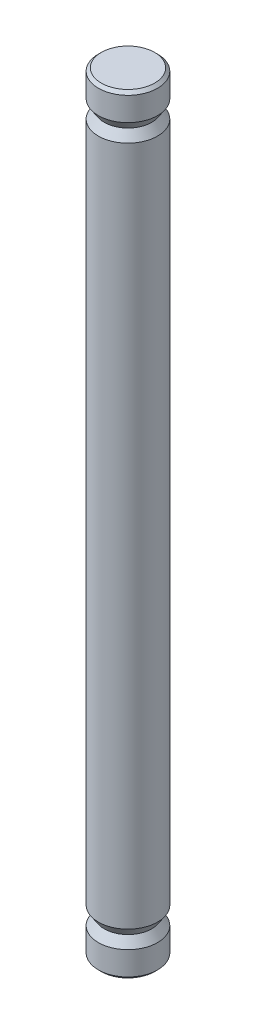
SolidWorks part; units mm, degrees
ref_plane "Plan de face" through (0, 0, 0) normal (0, 0, 1) x (1, 0, 0)
ref_plane "Plan de dessus" through (0, 0, 0) normal (0, 1, 0) x (1, 0, 0)
ref_plane "Plan de droite" through (0, 0, 0) normal (1, 0, 0) x (0, 0, -1)
sketch "Esquisse1" plane through (0, 0, 0) normal (0, 1, 0) x (1, 0, 0)
  circle A0 centre (0, 0) radius 2.5
  dimension "D1" = 5
extrude "Boss.-Extru.1" add sketch "Esquisse1" along normal blind 65
chamfer "Chanfrein1" distance 0.25 angle 45 2 edges at (0, 0, 2.5) (0, 65, 2.5)
ref_axis "Axe1" through (0, 64.75, 0) along (0, -1, 0)
sketch "Esquisse2" plane through (0, 0, 0) normal (0, 0, 1) x (1, 0, 0)
  line L0 (2.5, 62.75) -> (2, 62)
  line L1 (2.5, 0.25) -> (2.5, 64.75) construction
  line L2 (2, 62) -> (2.5, 61.25)
  line L4 (2.5, 62.75) -> (2.5, 61.25)
  line L5 (2.5, 32.5) -> (-2.5, 32.5) construction
  line L6 (-2.5, 64.75) -> (-2.5, 0.25) construction
  line L7 (2, 3) -> (2.5, 3.75)
  line L8 (2.5, 2.25) -> (2, 3)
  line L9 (2.5, 2.25) -> (2.5, 3.75)
  line L10 (2.25, 65) -> (-2.25, 65) construction
  dimension "D1" = 3
  dimension "D2" = 0.5
  dimension "D3" = 1.5
revolve "Enlèvement de matière-Révolution1" cut sketch "Esquisse2" angle 360 about axis through (0, 64.75, 0) along (0, -1, 0)
